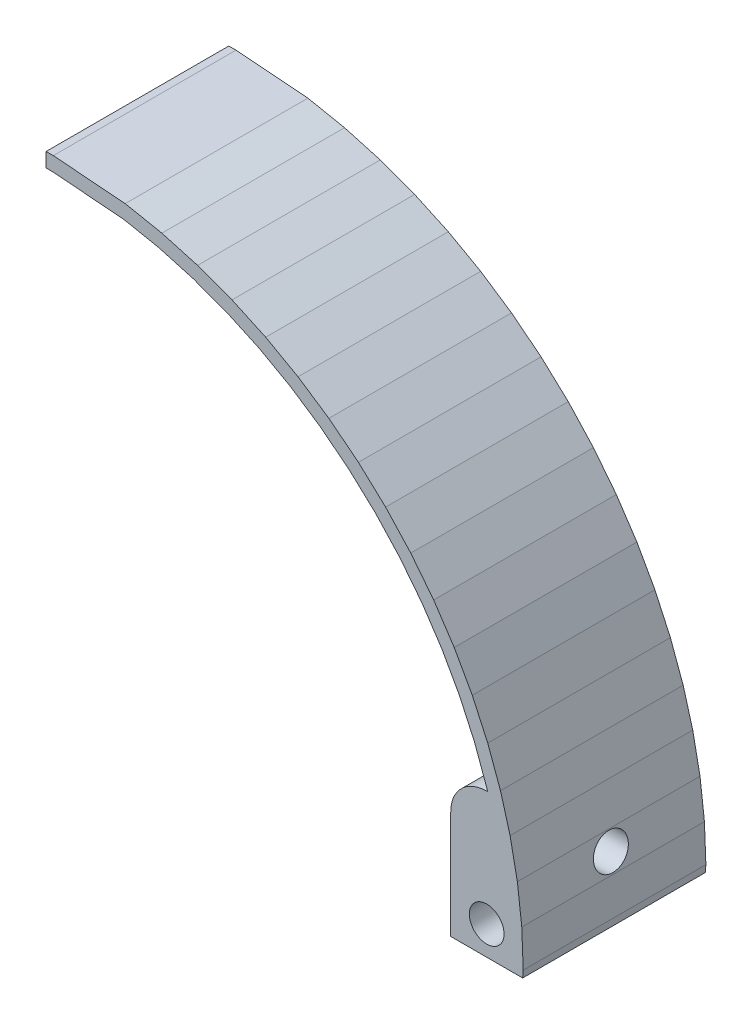
SolidWorks part; units mm, degrees
ref_plane "Front Plane" through (0, 0, 0) normal (0, 0, 1) x (1, 0, 0)
ref_plane "Top Plane" through (0, 0, 0) normal (0, 1, 0) x (1, 0, 0)
ref_plane "Right Plane" through (0, 0, 0) normal (1, 0, 0) x (0, 0, -1)
sketch "Sketch2" plane through (0, 0, 0) normal (0, 0, 1) x (1, 0, 0)
  line L0 (0, 0) -> (-0.1972, 5)
  line L1 (1.9984, 0.0788) -> (1.7982, 5.1579)
  line L2 (-0.1972, 5) -> (-0.7923, 10)
  line L3 (-0.7923, 10) -> (-1.7732, 14.9014)
  line L4 (-1.7732, 14.9014) -> (-3.0652, 19.4907)
  line L5 (-3.0652, 19.4907) -> (-4.7861, 24.1853)
  line L6 (-4.7861, 24.1853) -> (-6.87, 28.728)
  line L7 (-6.87, 28.728) -> (-9.3059, 33.0945)
  line L8 (-9.3059, 33.0945) -> (-12.075, 37.2521)
  line L9 (-12.075, 37.2521) -> (-15.1629, 41.1797)
  line L10 (-15.1629, 41.1797) -> (-18.5543, 44.8568)
  line L11 (-18.5543, 44.8568) -> (-22.2202, 48.2517)
  line L12 (-22.2202, 48.2517) -> (-26.2035, 51.3928)
  line L13 (-26.2035, 51.3928) -> (-30.3627, 54.168)
  line L14 (-30.3627, 54.168) -> (-34.723, 56.6051)
  line L15 (-34.723, 56.6051) -> (-39.2615, 58.6919)
  line L16 (-39.2615, 58.6919) -> (-43.9048, 60.401)
  line L17 (-43.9048, 60.401) -> (-48.7179, 61.7555)
  line L18 (-48.7179, 61.7555) -> (-53.6196, 62.7266)
  line L19 (-53.6196, 62.7266) -> (-63.5, 63.5)
  line L20 (1.7982, 5.1579) -> (1.1843, 10.3149)
  line L21 (1.1843, 10.3149) -> (0.1728, 15.3694)
  line L22 (0.1728, 15.3694) -> (-1.1609, 20.1068)
  line L23 (-1.1609, 20.1068) -> (-2.9354, 24.9476)
  line L24 (-2.9354, 24.9476) -> (-5.085, 29.6335)
  line L25 (-5.085, 29.6335) -> (-7.5976, 34.1376)
  line L26 (-7.5976, 34.1376) -> (-10.4541, 38.4263)
  line L27 (-10.4541, 38.4263) -> (-13.6393, 42.4778)
  line L28 (-13.6393, 42.4778) -> (-17.1376, 46.2707)
  line L29 (-17.1376, 46.2707) -> (-20.9195, 49.773)
  line L30 (-20.9195, 49.773) -> (-25.0274, 53.0124)
  line L31 (-25.0274, 53.0124) -> (-29.3181, 55.8753)
  line L32 (-29.3181, 55.8753) -> (-33.8159, 58.3893)
  line L33 (-33.8159, 58.3893) -> (-38.4971, 60.5418)
  line L34 (-38.4971, 60.5418) -> (-43.2876, 62.305)
  line L35 (-43.2876, 62.305) -> (-48.2519, 63.702)
  line L36 (-48.2519, 63.702) -> (-53.3463, 64.7113)
  line L37 (-53.3463, 64.7113) -> (-63.3439, 65.4939)
  line L38 (-63.3439, 65.4939) -> (-64.3439, 65.4939)
  line L39 (-64.3439, 65.4939) -> (-64.3439, 63.5)
  line L40 (-64.3439, 63.5) -> (-63.5, 63.5)
  line L41 (1.9984, 0.0788) -> (1.9208, -0.9136)
  line L42 (1.9208, -0.9136) -> (1.9227, -0.914)
  line L43 (0, -0.9136) -> (0, 0)
  line L44 (0, -0.9136) -> (1.9208, -0.9136)
  point P46 (0, 0)
  dimension "D1" = 2
  dimension "D2" = 5
  dimension "D3" = 5
  dimension "D4" = 4.6945
  dimension "D5" = 5
  dimension "D6" = 5
  dimension "D7" = 5
  dimension "D8" = 1
extrude "Boss-Extrude1" add sketch "Sketch2" along normal blind 25.4 contours L44 L43 L0 L2 L3 L4 L5 L6 L7 L8 L9 L10 L11 L12 L13 L14 L15 L16 L17 L18 L19 L40 L39 L38 L37 L36 L35 L34 L33 L32 L31 L30 L29 L28 L27 L26 L25 L24 L23 L22 L21 L20 L1 L41
sketch "Sketch10" plane through (0, 0, 25.4) normal (0, 0, 1) x (1, 0, 0)
  line L0 (1.9208, -0.9136) -> (1.9984, 0.0788)
  line L1 (1.9208, -0.9136) -> (-8.0792, -0.9136)
  line L2 (1.9208, -0.9136) -> (1.9208, 2.0488)
  line L3 (-0.8736, 19.0864) -> (-3.0792, 19.0864)
  line L4 (-8.0792, -0.9136) -> (-8.0792, 14.0864)
  line L5 (1.9984, 0.0788) -> (1.7982, 5.1579)
  line L6 (1.7982, 5.1579) -> (0.1728, 15.3694)
  line L7 (0.1728, 15.3694) -> (-0.8736, 19.0864)
  line L8 (0.1728, 15.3694) -> (-1.1609, 20.1068) construction
  arc A0 (-3.0792, 19.0864) -> (-8.0792, 14.0864) centre (-3.0792, 14.0864) ccw
  point P16 (-8.0792, 19.0864)
  dimension "D2" = 5
  dimension "D1" = 20
extrude "Boss-Extrude4" add sketch "Sketch10" against normal through all contours L1 L4 A0 L3 L7 L6 L5 L0
sketch "Sketch11" plane through (0, 0, 25.4) normal (0, 0, 1) x (1, 0, 0)
  line L0 (-3.0792, -0.9136) -> (-3.0792, 3.0864)
  line L1 (-8.0792, -0.9136) -> (1.9208, -0.9136) construction
  circle A0 centre (-3.0792, 3.0864) radius 2.413
  dimension "D2" = 4.826
  dimension "D1" = 4
extrude "Cut-Extrude5" cut sketch "Sketch11" against normal blind 10 contours A0
sketch "Sketch12" plane through (1.9984, 0.0788, 0) normal (0.9992, 0.0394, 0) x (0, 0, -1)
  line L0 (-12.7, 0) -> (-12.7, 5.083)
  line L1 (-25.4, 0) -> (0, 0) construction
  line L2 (-25.4, 5.083) -> (0, 5.083) construction
  line L4 (-12.7, 0) -> (-12.7, 7.7)
  circle A1 centre (-12.7, 7.7) radius 2.413
  dimension "D2" = 7.7
  dimension "D3" = 4.826
extrude "Cut-Extrude6" cut sketch "Sketch12" against normal through all
ref_plane "Plane3" through (0, 0, 12.7) normal (0, 0, -1) x (-1, 0, 0)
mirror "Mirror3" about plane through (0, 0, 12.7) normal (0, 0, -1) of "Cut-Extrude5"
sketch "Sketch15" plane through (0, 0, 10) normal (0, 0, -1) x (-1, 0, 0)
  line L1 (4.4878, 1.6606) -> (4.505, 4.495)
  line L2 (4.505, 4.495) -> (1.6707, 4.5122)
  line L3 (1.6707, 4.5122) -> (1.6534, 1.6778)
  line L4 (1.6534, 1.6778) -> (4.4878, 1.6606)
  circle A0 centre (3.0792, 3.0864) radius 1.4172 construction
extrude "Cut-Extrude7" cut sketch "Sketch15" against normal through all
